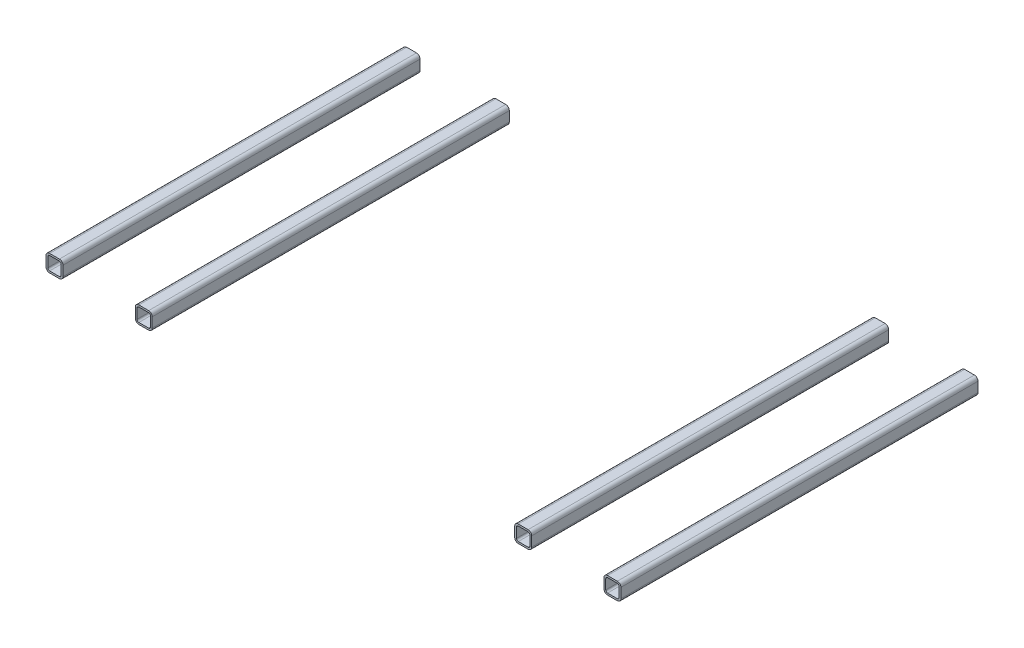
SolidWorks part; units mm, degrees
material "Beryllium"
ref_plane "Alzado" through (0, 0, 0) normal (0, 0, 1) x (1, 0, 0)
ref_plane "Planta" through (0, 0, 0) normal (0, 1, 0) x (1, 0, 0)
ref_plane "Vista lateral" through (0, 0, 0) normal (1, 0, 0) x (0, 0, -1)
sketch "Sketch1" plane through (0, 0, 0) normal (0, 1, 0) x (1, 0, 0)
  line L0 (-312.5, 0) -> (312.5, 0) construction
  line L1 (-312.5, -200) -> (-312.5, 200)
  line L2 (212.5, 0) -> (-212.5, 0) construction
  line L3 (-212.5, -200) -> (-212.5, 200)
  line L4 (0, 0) -> (0, 258.8125) construction
  line L5 (212.5, -200) -> (212.5, 200)
  line L6 (312.5, -200) -> (312.5, 200)
  point P4 (0, 0)
  point P8 (-312.5, 0)
  point P11 (0, 0)
  point P14 (-212.5, 0)
  dimension "D1" = 625
  dimension "D2" = 425
  dimension "D3" = 400
  dimension "D4" = 400
other "Square tube 20 X 20 X 2(2)"
ref_plane "Plane2" through (-312.5, 0, 200) normal (0, 0, -1) x (-1, 0, 0)
sketch "Sketch12" plane through (-312.5, 0, 200) normal (0, 0, -1) x (-1, 0, 0)
  line L0 (-5.5, -7.5) -> (5.5, -7.5)
  line L1 (-7.5, -5.5) -> (-7.5, 5.5)
  line L2 (5.5, 7.5) -> (-5.5, 7.5)
  line L3 (7.5, 5.5) -> (7.5, -5.5)
  line L4 (-5.5, -9.5) -> (5.5, -9.5)
  line L5 (-9.5, -5.5) -> (-9.5, 5.5)
  line L6 (5.5, 9.5) -> (-5.5, 9.5)
  line L7 (9.5, 5.5) -> (9.5, -5.5)
  arc A0 (9.5, 5.5) -> (5.5, 9.5) centre (5.5, 5.5) ccw
  arc A1 (5.5, -9.5) -> (9.5, -5.5) centre (5.5, -5.5) ccw
  arc A2 (-9.5, -5.5) -> (-5.5, -9.5) centre (-5.5, -5.5) ccw
  arc A3 (-5.5, 9.5) -> (-9.5, 5.5) centre (-5.5, 5.5) ccw
  arc A4 (-5.5, 7.5) -> (-7.5, 5.5) centre (-5.5, 5.5) ccw
  arc A5 (7.5, 5.5) -> (5.5, 7.5) centre (5.5, 5.5) ccw
  arc A6 (5.5, -7.5) -> (7.5, -5.5) centre (5.5, -5.5) ccw
  arc A7 (-7.5, -5.5) -> (-5.5, -7.5) centre (-5.5, -5.5) ccw
  point P0 (-9.5, 0)
  point P1 (9.5, 0)
  point P2 (0, 9.5)
  point P3 (0, -9.5)
  point P4 (0, 0)
  point P5 (-9.5, -9.5)
  point P6 (9.5, -9.5)
  point P7 (9.5, 9.5)
  point P8 (-9.5, 9.5)
  point P33 (0, 0)
  dimension "D1" = 4
  dimension "Thickness" = 2
  dimension "V_leg" = 19
